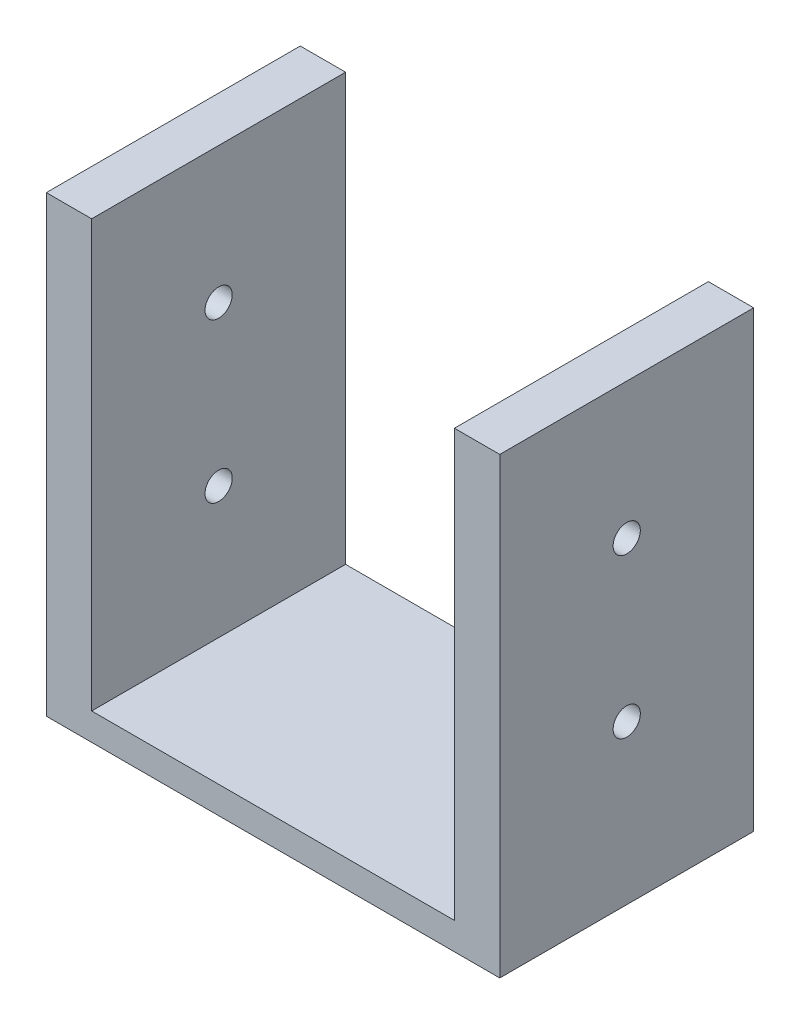
SolidWorks part; units mm, degrees
ref_plane "Alzado" through (0, 0, 0) normal (0, 0, 1) x (1, 0, 0)
ref_plane "Planta" through (0, 0, 0) normal (0, 1, 0) x (1, 0, 0)
ref_plane "Vista lateral" through (0, 0, 0) normal (1, 0, 0) x (0, 0, -1)
sketch "Croquis1" plane through (0, 0, 0) normal (0, 1, 0) x (1, 0, 0)
  line L1 (-25, 14) -> (25, 14)
  line L2 (-25, 14) -> (-25, -14)
  line L3 (-25, -14) -> (25, -14)
  line L4 (25, 14) -> (25, -14)
  line L5 (-25, 14) -> (25, -14) construction
  line L6 (-25, -14) -> (25, 14) construction
  line L7 (-25, 14) -> (-20, 14)
  line L8 (-25, 14) -> (-25, -14)
  line L9 (-25, -14) -> (-20, -14)
  line L10 (-20, 14) -> (-20, -14)
  line L11 (25, 14) -> (20, 14)
  line L12 (25, 14) -> (25, -14)
  line L13 (25, -14) -> (20, -14)
  line L14 (20, 14) -> (20, -14)
  point P0 (0, 0)
  dimension "D1" = 50
  dimension "D2" = 28
  dimension "D3" = 5
  dimension "D4" = 5
extrude "Saliente-Extruir1" add sketch "Croquis1" along normal blind 3 contours L10 L1 L2 L3 | L14 L1 L10 L3 | L1 L14 L3 L4
sketch "Croquis2" plane through (0, 3, 0) normal (0, 1, 0) x (1, 0, 0)
  line L0 (-25, -14) -> (25, -14) construction
  line L1 (-25, 14) -> (-20, 14)
  line L2 (-25, 14) -> (-25, -14)
  line L3 (-25, -14) -> (-20, -14)
  line L4 (-20, 14) -> (-20, -14)
  line L5 (-25, 14) -> (25, 14) construction
  line L6 (25, -14) -> (20, -14)
  line L7 (25, -14) -> (25, 14)
  line L8 (25, 14) -> (20, 14)
  line L9 (20, -14) -> (20, 14)
  dimension "D1" = 5
  dimension "D2" = 5
extrude "Saliente-Extruir2" add sketch "Croquis2" along normal blind 47
sketch "Croquis3" plane through (25, 0, 0) normal (1, 0, 0) x (0, 0, -1)
  line L0 (14, 0) -> (-14, 0) construction
  line L1 (-14, 50) -> (14, 50) construction
  circle A0 centre (0, 17.5) radius 1.5
  circle A1 centre (0, 35) radius 1.5
  dimension "D1" = 3
  dimension "D2" = 3
  dimension "D3" = 17.5
  dimension "D4" = 15
extrude "Cortar-Extruir1" cut sketch "Croquis3" against normal through all
